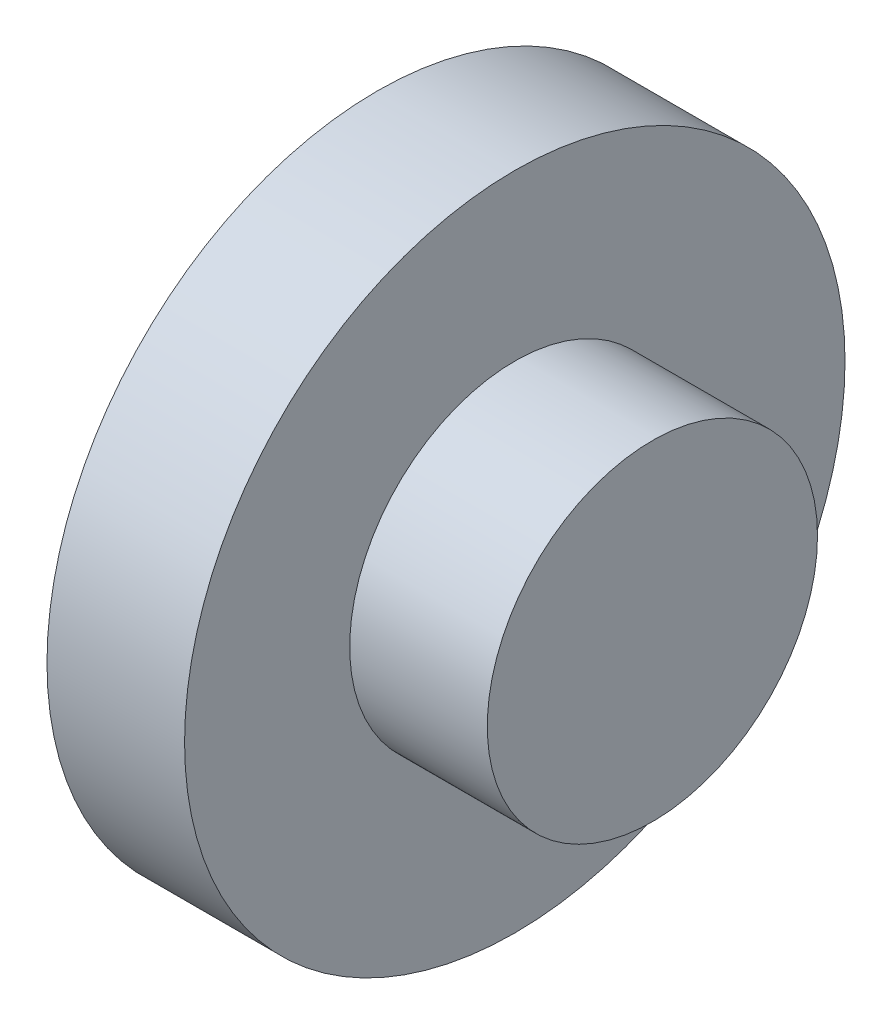
SolidWorks part; units mm, degrees
ref_plane "Front" through (0, 0, 0) normal (0, 0, 1) x (1, 0, 0)
ref_plane "Top" through (0, 0, 0) normal (0, 1, 0) x (1, 0, 0)
ref_plane "Right" through (0, 0, 0) normal (1, 0, 0) x (0, 0, -1)
sketch "草图1" plane through (0, 0, 0) normal (1, 0, 0) x (0, 0, -1)
  circle A0 centre (0, 0) radius 24
extrude "凸台-拉伸1" add sketch "草图1" along normal blind 10
sketch "草图2" plane through (10, 0, 0) normal (1, 0, 0) x (0, 0, -1)
  circle A0 centre (0, 0) radius 12
extrude "凸台-拉伸2" add sketch "草图2" along normal blind 10
